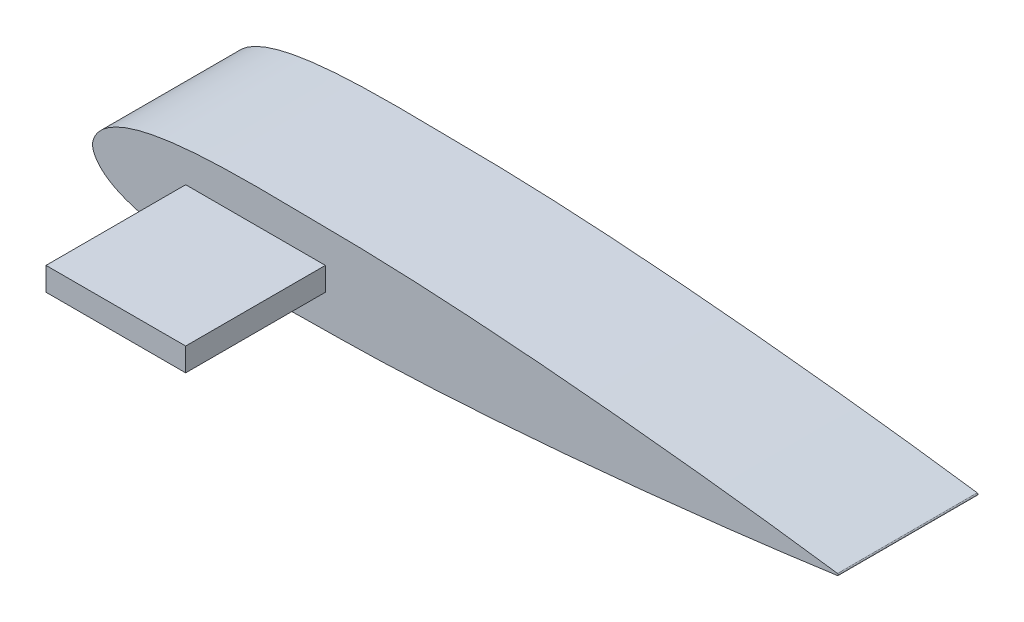
SolidWorks part; units mm, degrees
material "6061 Alloy"
ref_plane "Front" through (0, 0, 0) normal (0, 0, 1) x (1, 0, 0)
ref_plane "Top" through (0, 0, 0) normal (0, 1, 0) x (1, 0, 0)
ref_plane "Right" through (0, 0, 0) normal (1, 0, 0) x (0, 0, -1)
curve "Curve1"
  spline degree 3 poles (25.4, 0.032, 0) (24.9768, 0.0904, 0) (24.1307, 0.2071, 0) (22.8605, 0.3691, 0) (21.5905, 0.5229, 0) (20.3205, 0.6676, 0) (19.0504, 0.804, 0) (17.7804, 0.9321, 0) (16.5104, 1.0514, 0) (15.2404, 1.1606, 0) (13.9704, 1.2598, 0) (12.692, 1.3473, 0) (11.4135, 1.4221, 0) (10.1349, 1.4776, 0) (8.8649, 1.5185, 0) (7.8146, 1.5178, 0) (6.9766, 1.5373, 0) (6.35, 1.546, 0) (5.715, 1.5506, 0) (5.0799, 1.5478, 0) (4.4448, 1.5346, 0) (3.8095, 1.5078, 0) (3.1738, 1.462, 0) (2.5803, 1.3959, 0) (2.0289, 1.3055, 0) (1.6052, 1.2091, 0) (1.2675, 1.107, 0) (1.012, 1.0136, 0) (0.7549, 0.8965, 0) (0.4933, 0.743, 0) (0.2762, 0.5635, 0) (0.0851, 0.3233, 0) (-0.0556, 0, 0) (0.0851, -0.3233, 0) (0.2762, -0.5635, 0) (0.4933, -0.743, 0) (0.7549, -0.8965, 0) (1.012, -1.0136, 0) (1.2675, -1.107, 0) (1.6052, -1.2091, 0) (2.0289, -1.3055, 0) (2.5803, -1.3959, 0) (3.1738, -1.462, 0) (3.8095, -1.5078, 0) (4.4448, -1.5346, 0) (5.0799, -1.5478, 0) (5.715, -1.5506, 0) (6.35, -1.546, 0) (6.9766, -1.5373, 0) (7.8146, -1.5178, 0) (8.8649, -1.5185, 0) (10.1349, -1.4776, 0) (11.4135, -1.4221, 0) (12.692, -1.3473, 0) (13.9704, -1.2598, 0) (15.2404, -1.1606, 0) (16.5104, -1.0514, 0) (17.7804, -0.9321, 0) (19.0504, -0.804, 0) (20.3205, -0.6676, 0) (21.5905, -0.5229, 0) (22.8605, -0.3691, 0) (24.1307, -0.2071, 0) (24.9768, -0.0904, 0) (25.4, -0.032, 0) knots 0 0 0 0 0.024634 0.049243 0.07383 0.098397 0.122946 0.147479 0.171995 0.196494 0.220976 0.245442 0.27038 0.294813 0.319232 0.343642 0.35536 0.367566 0.379771 0.391975 0.404183 0.416399 0.428636 0.44092 0.450818 0.460843 0.465946 0.471149 0.476523 0.482208 0.488618 0.492568 0.5 0.507432 0.511382 0.517792 0.523477 0.528851 0.534054 0.539157 0.549182 0.55908 0.571364 0.583601 0.595817 0.608025 0.620229 0.632434 0.64464 0.656358 0.680768 0.705187 0.72962 0.754558 0.779024 0.803506 0.828005 0.852521 0.877054 0.901603 0.92617 0.950757 0.975366 1 1 1 1
sketch "Sketch1" plane through (0, 0, 0) normal (0, 0, 1) x (1, 0, 0)
  arc A0 (25.4, 0.032) -> (25.4, -0.032) centre (25.3956, 0) cw
  spline S0 degree 3 poles (854.2815, 4927.8246) (131.4617, -52.8735) (79.9606, -6.9131) (22.8605, 0.3691) (21.5905, 0.5229) (20.3205, 0.6676) (19.0504, 0.804) (17.7804, 0.9321) (16.5104, 1.0514) (15.2404, 1.1606) (13.9704, 1.2598) (12.692, 1.3473) (11.4135, 1.4221) (10.1349, 1.4776) (8.8649, 1.5185) (7.8146, 1.5178) (6.9766, 1.5373) (6.35, 1.546) (5.715, 1.5506) (5.0799, 1.5478) (4.4448, 1.5346) (3.8095, 1.5078) (3.1738, 1.462) (2.5803, 1.3959) (2.0289, 1.3055) (1.6052, 1.2091) (1.2675, 1.107) (1.012, 1.0136) (0.7549, 0.8965) (0.4933, 0.743) (0.2762, 0.5635) (0.0851, 0.3233) (-0.0556, 0) (0.0851, -0.3233) (0.2762, -0.5635) (0.4933, -0.743) (0.7549, -0.8965) (1.012, -1.0136) (1.2675, -1.107) (1.6052, -1.2091) (2.0289, -1.3055) (2.5803, -1.3959) (3.1738, -1.462) (3.8095, -1.5078) (4.4448, -1.5346) (5.0799, -1.5478) (5.715, -1.5506) (6.35, -1.546) (6.9766, -1.5373) (7.8146, -1.5178) (8.8649, -1.5185) (10.1349, -1.4776) (11.4135, -1.4221) (12.692, -1.3473) (13.9704, -1.2598) (15.2404, -1.1606) (16.5104, -1.0514) (17.7804, -0.9321) (19.0504, -0.804) (20.3205, -0.6676) (21.5905, -0.5229) (22.8605, -0.3691) (79.9605, 6.9131) (131.4614, 52.8733) (854.2757, -4927.7847) knots -3.245108 -3.245108 -3.245108 -3.245108 0.024634 0.049243 0.07383 0.098397 0.122946 0.147479 0.171995 0.196494 0.220976 0.245442 0.27038 0.294813 0.319232 0.343642 0.35536 0.367566 0.379771 0.391975 0.404183 0.416399 0.428636 0.44092 0.450818 0.460843 0.465946 0.471149 0.476523 0.482208 0.488618 0.492568 0.5 0.507432 0.511382 0.517792 0.523477 0.528851 0.534054 0.539157 0.549182 0.55908 0.571364 0.583601 0.595817 0.608025 0.620229 0.632434 0.64464 0.656358 0.680768 0.705187 0.72962 0.754558 0.779024 0.803506 0.828005 0.852521 0.877054 0.901603 0.92617 0.950757 0.975366 4.2451 4.2451 4.2451 4.2451 only from (25.4, 0.032) to (25.4, -0.032) construction
  spline S1 degree 3 poles (25.4, 0.032) (24.9768, 0.0904) (24.1307, 0.2071) (22.8605, 0.3691) (21.5905, 0.5229) (20.3205, 0.6676) (19.0504, 0.804) (17.7804, 0.9321) (16.5104, 1.0514) (15.2404, 1.1606) (13.9704, 1.2598) (12.692, 1.3473) (11.4135, 1.4221) (10.1349, 1.4776) (8.8649, 1.5185) (7.8146, 1.5178) (6.9766, 1.5373) (6.35, 1.546) (5.715, 1.5506) (5.0799, 1.5478) (4.4448, 1.5346) (3.8095, 1.5078) (3.1738, 1.462) (2.5803, 1.3959) (2.0289, 1.3055) (1.6052, 1.2091) (1.2675, 1.107) (1.012, 1.0136) (0.7549, 0.8965) (0.4933, 0.743) (0.2762, 0.5635) (0.0851, 0.3233) (-0.0556, 0) (0.0851, -0.3233) (0.2762, -0.5635) (0.4933, -0.743) (0.7549, -0.8965) (1.012, -1.0136) (1.2675, -1.107) (1.6052, -1.2091) (2.0289, -1.3055) (2.5803, -1.3959) (3.1738, -1.462) (3.8095, -1.5078) (4.4448, -1.5346) (5.0799, -1.5478) (5.715, -1.5506) (6.35, -1.546) (6.9766, -1.5373) (7.8146, -1.5178) (8.8649, -1.5185) (10.1349, -1.4776) (11.4135, -1.4221) (12.692, -1.3473) (13.9704, -1.2598) (15.2404, -1.1606) (16.5104, -1.0514) (17.7804, -0.9321) (19.0504, -0.804) (20.3205, -0.6676) (21.5905, -0.5229) (22.8605, -0.3691) (24.1307, -0.2071) (24.9768, -0.0904) (25.4, -0.032) knots 0 0 0 0 0.024634 0.049243 0.07383 0.098397 0.122946 0.147479 0.171995 0.196494 0.220976 0.245442 0.27038 0.294813 0.319232 0.343642 0.35536 0.367566 0.379771 0.391975 0.404183 0.416399 0.428636 0.44092 0.450818 0.460843 0.465946 0.471149 0.476523 0.482208 0.488618 0.492568 0.5 0.507432 0.511382 0.517792 0.523477 0.528851 0.534054 0.539157 0.549182 0.55908 0.571364 0.583601 0.595817 0.608025 0.620229 0.632434 0.64464 0.656358 0.680768 0.705187 0.72962 0.754558 0.779024 0.803506 0.828005 0.852521 0.877054 0.901603 0.92617 0.950757 0.975366 1 1 1 1
extrude "Boss-Extrude1" add sketch "Sketch1" along normal blind 4.7625 contours S1 A0
scale "Scale2" scale about origin uniform scaling yes scale factor 4
sketch "Sketch8" plane through (0, 0, 19.05) normal (0, 0, 1) x (1, 0, 0)
  line L1 (12.7, 1.5875) -> (31.75, 1.5875)
  line L2 (12.7, 1.5875) -> (12.7, -1.5875)
  line L3 (12.7, -1.5875) -> (31.75, -1.5875)
  line L4 (31.75, 1.5875) -> (31.75, -1.5875)
  line L5 (12.7, 1.5875) -> (31.75, -1.5875) construction
  line L6 (12.7, -1.5875) -> (31.75, 1.5875) construction
  point P0 (22.225, 0)
  point P5 (0, 0)
  dimension "D1" = 19.05
  dimension "D2" = 3.175
  dimension "D3" = 22.225
extrude "Boss-Extrude2" add sketch "Sketch8" along normal blind 19.05
sketch "Sketch9" plane through (0, 0, 0) normal (0, 0, -1) x (-1, 0, 0)
  circle A0 centre (-22.225, 0) radius 5.5562
  point P2 (0, 0)
  dimension "D1" = 11.1125
  dimension "D2" = 22.225
extrude "Cut-Extrude2" cut sketch "Sketch9" against normal blind 12.7 contours A0
hole_wizard "#8 Clearance Hole1" positions "Sketch14" profile "Sketch13" hole size "#8" standard "ANSI Inch"
sketch "Sketch14" plane through (0, 0, 0) normal (1, 0, 0) x (0, 0, -1)
  point P0 (-6.35, 0)
  point P4 (0, 0)
  dimension "D1" = 6.35
sketch "Sketch13" plane through (0, 0, 6.35) normal (0, 1, 0) x (0, 0, 1)
  line L0 (0, 0) -> (0, 16.6687)
  line L1 (0, 16.6687) -> (2.1526, 16.6687)
  line L2 (2.1526, 16.6687) -> (2.1526, 0)
  line L5 (2.1526, 0) -> (0, 0)
  line L11 (0, -6.35) -> (0, 107.95) construction
  dimension "Thru Hole Dia." = 4.3053
  dimension "Thru Hole Depth" = 16.6687
